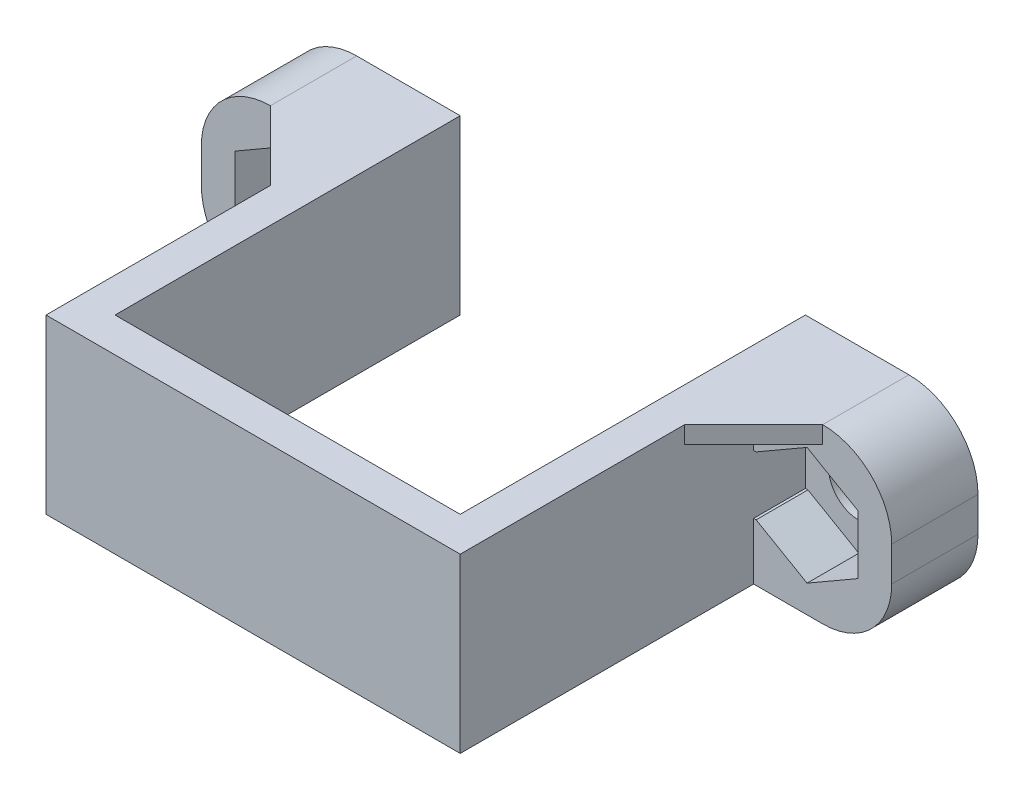
SolidWorks part; units mm, degrees
ref_plane "Спереди" through (0, 0, 0) normal (0, 0, 1) x (1, 0, 0)
ref_plane "Сверху" through (0, 0, 0) normal (0, 1, 0) x (1, 0, 0)
ref_plane "Справа" through (0, 0, 0) normal (1, 0, 0) x (0, 0, -1)
sketch "Эскиз1" plane through (0, 0, 0) normal (0, 1, 0) x (1, 0, 0)
  line L0 (-10, 0) -> (10, 0)
  line L1 (-12, -2) -> (12, -2)
  line L2 (-10, 0) -> (-10, 20)
  line L3 (10, 0) -> (10, 20)
  line L5 (-10, 20) -> (-20, 20)
  line L6 (10, 20) -> (20, 20)
  line L7 (-20, 20) -> (-20, 18)
  line L8 (20, 20) -> (20, 18)
  line L9 (20, 18) -> (12, 18)
  line L10 (12, -2) -> (12, 18)
  line L11 (-12, -2) -> (-12, 18)
  line L12 (-12, 18) -> (-20, 18)
  point P4 (0, 0)
  point P7 (0, -2)
  point P12 (0, 21.6587)
  dimension "D1" = 20
  dimension "D2" = 24
  dimension "D3" = 2
  dimension "D4" = 20
  dimension "D6" = 10
  dimension "D7" = 10
  dimension "D8" = 2
extrude "Бобышка-Вытянуть1" add sketch "Эскиз1" along normal blind 10
fillet "Скругление1" radius 4 4 edges at (-20, 0, -19) (20, 0, -19) (20, 10, -19) (-20, 10, -19)
sketch "Эскиз2" plane through (0, 0, -18) normal (0, 0, 1) x (1, 0, 0)
  line L0 (20, 6) -> (20, 4) construction
  line L1 (12, 0) -> (16, 0) construction
  line L2 (12, 10) -> (16, 10) construction
  line L3 (12, 10) -> (12, 0) construction
  line L4 (-12, 10) -> (-12, 0) construction
  line L5 (-16, 0) -> (-12, 0) construction
  line L6 (-20, 6) -> (-20, 4) construction
  line L7 (-16, 10) -> (-12, 10) construction
  line L8 (20, 6) -> (20, 4)
  line L9 (12, 0) -> (16, 0)
  line L10 (12, 10) -> (16, 10)
  line L11 (12, 10) -> (12, 0)
  line L12 (-12, 10) -> (-12, 0)
  line L13 (-16, 0) -> (-12, 0)
  line L14 (-20, 6) -> (-20, 4)
  line L15 (-16, 10) -> (-12, 10)
  line L16 (-15.095, 5) -> (15.095, 5)
  line L17 (-12, 10) -> (12, 10) construction
  line L18 (-12.145, 6.7032) -> (-12, 6.7032)
  line L19 (-15.095, 8.4064) -> (-18.045, 6.7032)
  line L20 (-18.045, 6.7032) -> (-18.045, 3.2968)
  line L21 (-18.045, 3.2968) -> (-15.095, 1.5936)
  line L22 (-15.095, 1.5936) -> (-12.145, 3.2968)
  line L23 (12.145, 6.7032) -> (12, 6.7032)
  line L24 (-12.145, 6.7032) -> (-15.095, 8.4064)
  line L25 (15.095, 1.5936) -> (18.045, 3.2968)
  line L26 (18.045, 3.2968) -> (18.045, 6.7032)
  line L27 (18.045, 6.7032) -> (15.095, 8.4064)
  line L28 (15.095, 8.4064) -> (12.145, 6.7032)
  line L30 (12.145, 3.2968) -> (15.095, 1.5936)
  line L31 (-12.145, 3.2968) -> (-12, 3.2968)
  line L32 (12.145, 3.2968) -> (12, 3.2968)
  line L33 (-12.145, 3.2968) -> (-12.145, 5) [skipped]
  line L35 (12.145, 5) -> (12.145, 3.2968) [skipped]
  arc A0 (20, 6) -> (16, 10) centre (16, 6) ccw construction
  arc A1 (16, 0) -> (20, 4) centre (16, 4) ccw construction
  arc A2 (-20, 4) -> (-16, 0) centre (-16, 4) ccw construction
  arc A3 (-16, 10) -> (-20, 6) centre (-16, 6) ccw construction
  arc A4 (20, 6) -> (16, 10) centre (16, 6) ccw
  arc A5 (16, 0) -> (20, 4) centre (16, 4) ccw
  arc A6 (-20, 4) -> (-16, 0) centre (-16, 4) ccw
  arc A7 (-16, 10) -> (-20, 6) centre (-16, 6) ccw
  circle A8 centre (-15.095, 5) radius 2.95 construction
  circle A9 centre (15.095, 5) radius 2.95 construction
  point P19 (0, 5)
  point P22 (0, 10)
  line M2 (-20, 6) -> (-20, 4)
  arc M3 (-20, 4) -> (-16, 0) centre (-16, 4) ccw
  line M4 (-16, 0) -> (-12, 0)
  line M5 (-12, 0) -> (-12, 10)
  line M6 (-12, 10) -> (-16, 10)
  arc M7 (-16, 10) -> (-20, 6) centre (-16, 6) ccw
  dimension "D1" = 30.19
extrude "Бобышка-Вытянуть2" add sketch "Эскиз2" along normal blind 3 contours L31 L22 L21 L20 L19 L24 L18 M5 M6 M7 M2 M3 M4 | L9 A5 L8 A4 L10 L11 L23 L28 L27 L26 L25 L30 L32
sketch "Эскиз3" plane through (0, 0, -18) normal (0, 0, 1) x (1, 0, 0)
  circle A0 centre (-15.095, 5) radius 1.75
  circle A1 centre (15.095, 5) radius 1.75
  dimension "D1" = 3.5
  dimension "D2" = 3.5
extrude "Вырез-Вытянуть1" cut sketch "Эскиз3" against normal through all
sketch "Эскиз4" plane through (0, 10, 0) normal (0, 1, 0) x (1, 0, 0)
  line L0 (-16, 15) -> (-12, 11)
  line L1 (-12, 15) -> (-12, -2) construction
  line L2 (-12, 11) -> (-12, 15)
  line L3 (-12, 15) -> (-16, 15)
  line L4 (0, 0) -> (0, 22.4566) construction
  line L5 (10, 0) -> (-10, 0) construction
  line L6 (12, 15) -> (16, 15)
  line L7 (12, 11) -> (12, 15)
  line L8 (16, 15) -> (12, 11)
extrude "Бобышка-Вытянуть3" add sketch "Эскиз4" against normal blind 1
